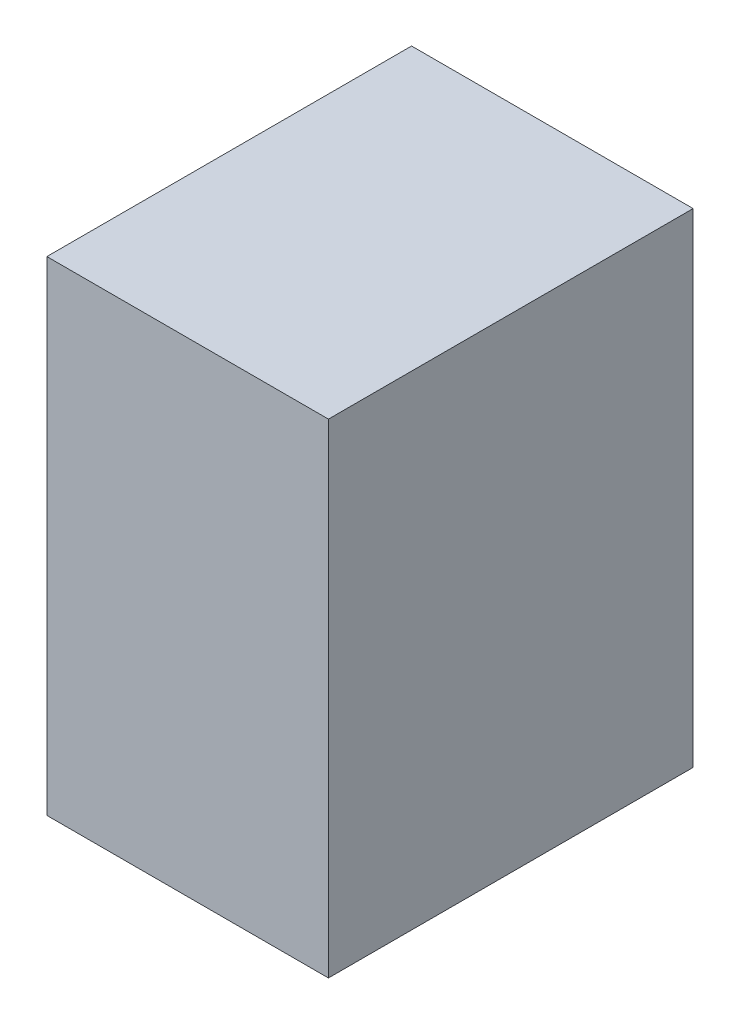
SolidWorks part; units mm, degrees
ref_plane "Спереди" through (0, 0, 0) normal (0, 0, 1) x (1, 0, 0)
ref_plane "Сверху" through (0, 0, 0) normal (0, 1, 0) x (1, 0, 0)
ref_plane "Справа" through (0, 0, 0) normal (1, 0, 0) x (0, 0, -1)
sketch "Эскиз1" plane through (0, 0, 0) normal (0, 1, 0) x (1, 0, 0)
  line L1 (-1276.3571, 2590.6252) -> (-1066.3571, 2590.6252)
  line L2 (-1276.3571, 2590.6252) -> (-1276.3571, 2318.6252)
  line L3 (-1276.3571, 2318.6252) -> (-1066.3571, 2318.6252)
  line L4 (-1066.3571, 2590.6252) -> (-1066.3571, 2318.6252)
  dimension "D1" = 210
  dimension "D2" = 272
extrude "Бобышка-Вытянуть1" add sketch "Эскиз1" along normal blind 361
